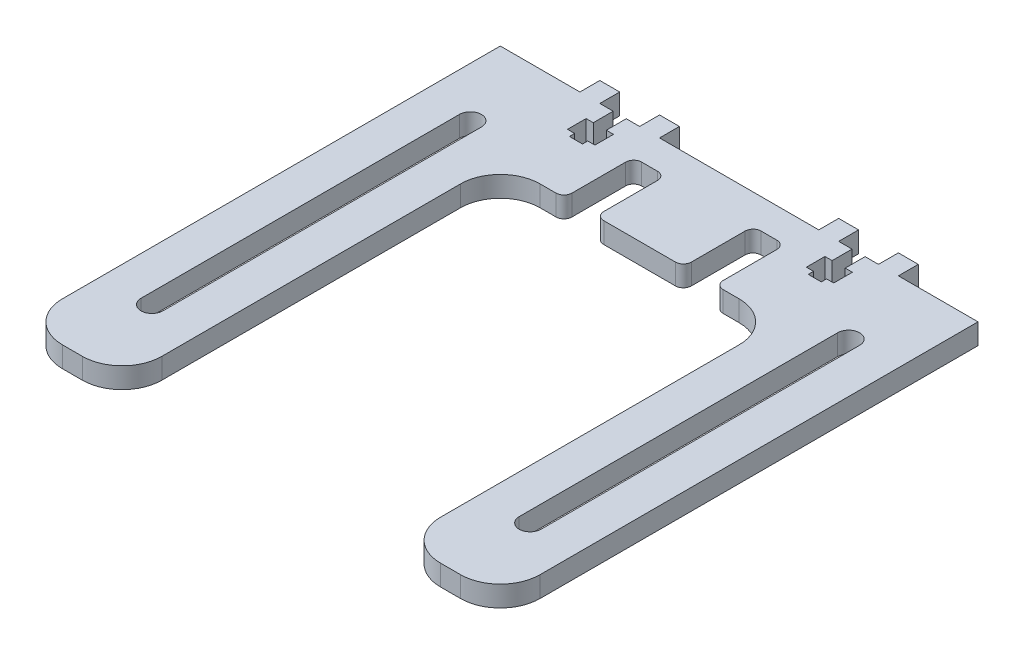
SolidWorks part; units mm, degrees
material "Acrylic (BLUE)"
ref_plane "Front Plane" through (0, 0, 0) normal (0, 0, 1) x (1, 0, 0)
ref_plane "Top Plane" through (0, 0, 0) normal (0, 1, 0) x (1, 0, 0)
ref_plane "Right Plane" through (0, 0, 0) normal (1, 0, 0) x (0, 0, -1)
sketch "Sketch1" plane through (0, 0, 0) normal (0, 1, 0) x (1, 0, 0)
  line L0 (44.45, -152.4) -> (76.2, -152.4)
  line L1 (-76.2, 0) -> (76.2, 0)
  line L2 (-76.2, 0) -> (-76.2, -152.4)
  line L3 (-76.2, -152.4) -> (-44.45, -152.4)
  line L4 (76.2, 0) -> (76.2, -152.4)
  line L5 (0, 0) -> (0, -31.75) construction
  line L6 (-44.45, -152.4) -> (-44.45, -31.75)
  line L7 (-44.45, -31.75) -> (44.45, -31.75)
  line L8 (44.45, -152.4) -> (44.45, -31.75)
  dimension "D1" = 152.4
  dimension "D2" = 31.75
  dimension "D3" = 152.4
  dimension "D4" = 31.75
extrude "Boss-Extrude1" add sketch "Sketch1" along normal blind 6.604
sketch "Sketch2" plane through (0, 6.604, 0) normal (0, 1, 0) x (1, 0, 0)
  line L0 (-60.325, -25.4) -> (-60.325, -127) construction
  line L1 (-56.8325, -25.4) -> (-56.8325, -127)
  line L2 (-63.8175, -25.4) -> (-63.8175, -127)
  line L3 (-76.2, -152.4) -> (-44.45, -152.4) construction
  line L4 (76.2, 0) -> (-76.2, 0) construction
  line L5 (0, 0) -> (0, -152.4) construction
  line L6 (60.325, -25.4) -> (60.325, -127) construction
  line L7 (56.8325, -25.4) -> (56.8325, -127)
  line L8 (63.8175, -25.4) -> (63.8175, -127)
  arc A0 (-56.8325, -25.4) -> (-63.8175, -25.4) centre (-60.325, -25.4) ccw
  arc A1 (-63.8175, -127) -> (-56.8325, -127) centre (-60.325, -127) ccw
  arc A2 (56.8325, -25.4) -> (63.8175, -25.4) centre (60.325, -25.4) cw
  arc A3 (63.8175, -127) -> (56.8325, -127) centre (60.325, -127) cw
  point P2 (-60.325, -76.2)
  point P7 (-60.325, -152.4)
  point P17 (60.325, -76.2)
  point P22 (60.325, -152.4)
  dimension "D3" = 6.985
  dimension "D1" = 25.4
  dimension "D2" = 25.4
extrude "Cut-Extrude1" cut sketch "Sketch2" against normal through all contours L1 A1 L2 A0
fillet "Fillet1" radius 12.7 6 edges at (-44.45, 3.302, 152.4) (-76.2, 3.302, 152.4) (76.2, 3.302, 152.4) (44.45, 3.302, 152.4) (44.45, 3.302, 31.75) (-44.45, 3.302, 31.75)
sketch "Sketch3" plane through (0, 6.604, 0) normal (0, 1, 0) x (1, 0, 0)
  line L0 (76.2, 0) -> (-76.2, 0) construction
  line L1 (-76.2, 0) -> (-76.2, -139.7) construction
  line L2 (-50.8, 0) -> (-76.2, 0) construction
  line L3 (50.8, 0) -> (76.2, 0) construction
  line B0 (-40.1828, 0) -> (-40.1828, -6.35)
  line B1 (-40.1828, -6.35) -> (-42.4688, -6.35)
  line B2 (-42.4688, -6.35) -> (-42.4688, -12.2936)
  line B3 (-42.4688, -12.2936) -> (-40.1828, -12.2936)
  line B4 (-40.1828, -12.2936) -> (-40.1828, -13.97)
  line B5 (-40.1828, -13.97) -> (-36.0172, -13.97)
  line B6 (-36.0172, -13.97) -> (-36.0172, -12.2936)
  line B7 (-36.0172, -12.2936) -> (-33.7312, -12.2936)
  line B8 (-33.7312, -12.2936) -> (-33.7312, -6.35)
  line B9 (-33.7312, -6.35) -> (-36.0172, -6.35)
  line B10 (-36.0172, -6.35) -> (-36.0172, 0)
  line B11 (-36.0172, 0) -> (-31.75, 0)
  line B12 (-31.75, 0) -> (-31.75, 6.35)
  line B13 (-31.75, 6.35) -> (-25.4, 6.35)
  line B14 (-25.4, 6.35) -> (-25.4, 0)
  line B15 (-44.45, 0) -> (-44.45, 6.35)
  line B16 (-44.45, 6.35) -> (-50.8, 6.35)
  line B17 (-50.8, 6.35) -> (-50.8, 0)
  line B18 (-36.0172, 0) -> (-40.1828, 0) construction
  line B19 (36.0172, 0) -> (36.0172, -6.35)
  line B20 (36.0172, -6.35) -> (33.7312, -6.35)
  line B21 (33.7312, -6.35) -> (33.7312, -12.2936)
  line B22 (33.7312, -12.2936) -> (36.0172, -12.2936)
  line B23 (36.0172, -12.2936) -> (36.0172, -13.97)
  line B24 (36.0172, -13.97) -> (40.1828, -13.97)
  line B25 (40.1828, -13.97) -> (40.1828, -12.2936)
  line B26 (40.1828, -12.2936) -> (42.4688, -12.2936)
  line B27 (42.4688, -12.2936) -> (42.4688, -6.35)
  line B28 (42.4688, -6.35) -> (40.1828, -6.35)
  line B29 (40.1828, -6.35) -> (40.1828, 0)
  line B30 (40.1828, 0) -> (44.45, 0)
  line B31 (44.45, 0) -> (44.45, 6.35)
  line B32 (44.45, 6.35) -> (50.8, 6.35)
  line B33 (50.8, 6.35) -> (50.8, 0)
  line B34 (36.0172, 0) -> (31.75, 0)
  line B35 (31.75, 0) -> (31.75, 6.35)
  line B36 (31.75, 6.35) -> (25.4, 6.35)
  line B37 (25.4, 6.35) -> (25.4, 0)
  line B38 (40.1828, 0) -> (36.0172, 0) construction
  dimension "D1" = 76.2
sketch_block_instance "NUT_HOLE-1"
sketch_block "NUT_HOLE" parameters "D1"=6.35, "D2"=4.1656, "D3"=25.4, "D4"=6.35, "D5"=8.7376, "D6"=5.9436, "D7"=6.35, "D8"=20.32
sketch_block_instance "NUT_HOLE-2"
sketch "Sketch4" plane through (0, 6.604, 0) normal (0, 1, 0) x (1, 0, 0)
  line L0 (-40.1828, 0) -> (-40.1828, -6.35) construction
  line L1 (-40.1828, -6.35) -> (-42.4688, -6.35) construction
  line L2 (-42.4688, -6.35) -> (-42.4688, -12.2936) construction
  line L3 (-42.4688, -12.2936) -> (-40.1828, -12.2936) construction
  line L4 (-40.1828, -12.2936) -> (-40.1828, -13.97) construction
  line L5 (-36.0172, -6.35) -> (-36.0172, 0) construction
  line L6 (-33.7312, -6.35) -> (-36.0172, -6.35) construction
  line L7 (-33.7312, -12.2936) -> (-33.7312, -6.35) construction
  line L8 (-36.0172, -12.2936) -> (-33.7312, -12.2936) construction
  line L9 (-36.0172, -13.97) -> (-36.0172, -12.2936) construction
  line L10 (-40.1828, -13.97) -> (-36.0172, -13.97) construction
  line L11 (-40.1828, 0) -> (-40.1828, -6.35)
  line L12 (-40.1828, -6.35) -> (-42.4688, -6.35)
  line L13 (-42.4688, -6.35) -> (-42.4688, -12.2936)
  line L14 (-42.4688, -12.2936) -> (-40.1828, -12.2936)
  line L15 (-40.1828, -12.2936) -> (-40.1828, -13.97)
  line L16 (-36.0172, -6.35) -> (-36.0172, 0)
  line L17 (-33.7312, -6.35) -> (-36.0172, -6.35)
  line L18 (-33.7312, -12.2936) -> (-33.7312, -6.35)
  line L19 (-36.0172, -12.2936) -> (-33.7312, -12.2936)
  line L20 (-36.0172, -13.97) -> (-36.0172, -12.2936)
  line L21 (-40.1828, -13.97) -> (-36.0172, -13.97)
  line L22 (36.0172, 0) -> (36.0172, -6.35) construction
  line L23 (36.0172, -6.35) -> (33.7312, -6.35) construction
  line L24 (33.7312, -6.35) -> (33.7312, -12.2936) construction
  line L25 (33.7312, -12.2936) -> (36.0172, -12.2936) construction
  line L26 (36.0172, -12.2936) -> (36.0172, -13.97) construction
  line L27 (36.0172, -13.97) -> (40.1828, -13.97) construction
  line L28 (40.1828, -13.97) -> (40.1828, -12.2936) construction
  line L29 (40.1828, -12.2936) -> (42.4688, -12.2936) construction
  line L30 (42.4688, -12.2936) -> (42.4688, -6.35) construction
  line L31 (42.4688, -6.35) -> (40.1828, -6.35) construction
  line L32 (40.1828, -6.35) -> (40.1828, 0) construction
  line L33 (36.0172, 0) -> (36.0172, -6.35)
  line L34 (36.0172, -6.35) -> (33.7312, -6.35)
  line L35 (33.7312, -6.35) -> (33.7312, -12.2936)
  line L36 (33.7312, -12.2936) -> (36.0172, -12.2936)
  line L37 (36.0172, -12.2936) -> (36.0172, -13.97)
  line L38 (36.0172, -13.97) -> (40.1828, -13.97)
  line L39 (40.1828, -13.97) -> (40.1828, -12.2936)
  line L40 (40.1828, -12.2936) -> (42.4688, -12.2936)
  line L41 (42.4688, -12.2936) -> (42.4688, -6.35)
  line L42 (42.4688, -6.35) -> (40.1828, -6.35)
  line L43 (40.1828, -6.35) -> (40.1828, 0)
  line L44 (-40.1828, 0) -> (-36.0172, 0)
  line L45 (36.0172, 0) -> (40.1828, 0)
  point P0 (-40.1828, -12.2936)
extrude "Cut-Extrude2" cut sketch "Sketch4" against normal through all
sketch "Sketch5" plane through (0, 6.604, 0) normal (0, 1, 0) x (1, 0, 0)
  line L0 (-50.8, 6.35) -> (-50.8, 0) construction
  line L1 (-44.45, 6.35) -> (-50.8, 6.35) construction
  line L2 (-44.45, 0) -> (-44.45, 6.35) construction
  line L3 (-31.75, 0) -> (-31.75, 6.35) construction
  line L4 (-31.75, 6.35) -> (-25.4, 6.35) construction
  line L5 (-25.4, 6.35) -> (-25.4, 0) construction
  line L6 (50.8, 6.35) -> (50.8, 0) construction
  line L7 (44.45, 6.35) -> (50.8, 6.35) construction
  line L8 (44.45, 0) -> (44.45, 6.35) construction
  line L9 (31.75, 6.35) -> (25.4, 6.35) construction
  line L10 (25.4, 6.35) -> (25.4, 0) construction
  line L11 (31.75, 0) -> (31.75, 6.35) construction
  line L12 (-50.8, 6.35) -> (-50.8, 0)
  line L13 (-44.45, 6.35) -> (-50.8, 6.35)
  line L14 (-44.45, 0) -> (-44.45, 6.35)
  line L15 (-31.75, 0) -> (-31.75, 6.35)
  line L16 (-31.75, 6.35) -> (-25.4, 6.35)
  line L17 (-25.4, 6.35) -> (-25.4, 0)
  line L18 (50.8, 6.35) -> (50.8, 0)
  line L19 (44.45, 6.35) -> (50.8, 6.35)
  line L20 (44.45, 0) -> (44.45, 6.35)
  line L21 (31.75, 6.35) -> (25.4, 6.35)
  line L22 (25.4, 6.35) -> (25.4, 0)
  line L23 (31.75, 0) -> (31.75, 6.35)
  line L24 (-50.8, 0) -> (-44.45, 0)
  line L25 (-31.75, 0) -> (-25.4, 0)
  line L26 (25.4, 0) -> (31.75, 0)
  line L27 (44.45, 0) -> (50.8, 0)
extrude "Boss-Extrude2" add sketch "Sketch5" against normal up to surface (6.604 mm away) up to face at (60.325, 0, 76.2)
sketch "Sketch6" plane through (0, 6.604, 0) normal (0, 1, 0) x (1, 0, 0)
  line L0 (-31.75, -31.75) -> (31.75, -31.75) construction
  line L1 (-24.13, -31.75) -> (-13.97, -31.75)
  line L2 (-24.13, -31.75) -> (-24.13, -9.525)
  line L3 (-24.13, -9.525) -> (-13.97, -9.525)
  line L4 (-13.97, -31.75) -> (-13.97, -9.525)
  line L5 (-19.05, -9.525) -> (-19.05, 0) construction
  line L6 (13.97, -31.75) -> (24.13, -31.75)
  line L7 (13.97, -31.75) -> (13.97, -9.525)
  line L8 (13.97, -9.525) -> (24.13, -9.525)
  line L9 (24.13, -31.75) -> (24.13, -9.525)
  line L10 (25.4, 0) -> (-25.4, 0) construction
  line L11 (19.05, -9.525) -> (19.05, 0) construction
  dimension "D1" = 19.05
  dimension "D2" = 19.05
  dimension "D3" = 10.16
  dimension "D4" = 22.225
extrude "Cut-Extrude5" cut sketch "Sketch6" against normal through all
fillet "Fillet2" radius 2.54 8 edges at (13.97, 3.302, 9.525) (13.97, 3.302, 31.75) (24.13, 3.302, 31.75) (24.13, 3.302, 9.525) (-13.97, 3.302, 31.75) (-24.13, 3.302, 31.75) (-13.97, 3.302, 9.525) (-24.13, 3.302, 9.525)
other "Move Face1" [suppressed] parameters "D1"=0.0508
